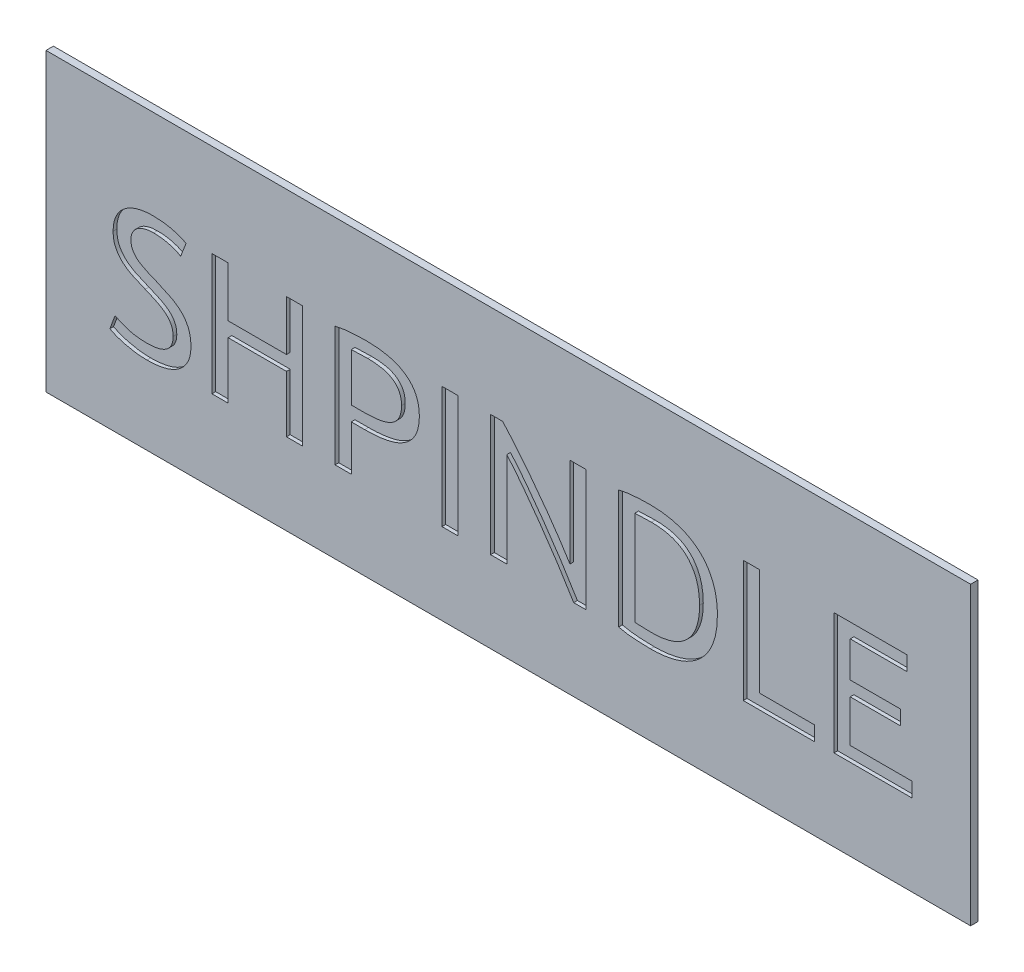
SolidWorks part; units mm, degrees
ref_plane "Front Plane" through (0, 0, 0) normal (0, 0, 1) x (1, 0, 0)
ref_plane "Top Plane" through (0, 0, 0) normal (0, 1, 0) x (1, 0, 0)
ref_plane "Right Plane" through (0, 0, 0) normal (1, 0, 0) x (0, 0, -1)
sketch "Sketch1" plane through (0, 0, 0) normal (0, 0, 1) x (1, 0, 0)
  line L1 (12.5, -4) -> (-12.5, -4)
  line L2 (12.5, -4) -> (12.5, 4)
  line L3 (12.5, 4) -> (-12.5, 4)
  line L4 (-12.5, -4) -> (-12.5, 4)
  line L5 (12.5, -4) -> (-12.5, 4) construction
  line L6 (12.5, 4) -> (-12.5, -4) construction
  point P0 (0, 0)
  dimension "D1" = 8
  dimension "D2" = 25
extrude "Boss-Extrude1" add sketch "Sketch1" along normal mid plane 0.2
sketch "Sketch2" plane through (0, 0, 0.1) normal (0, 0, 1) x (1, 0, 0)
  text T0 "SHPINDLE" font "Ubuntu" height in points 12
extrude "Cut-Extrude1" cut sketch "Sketch2" against normal blind 0.1
sketch "Sketch3" plane through (0, 0, 0.1) normal (0, 0, 1) x (1, 0, 0)
  text T0 "MOTOR  X" font "Ubuntu" height in points 12
extrude "Cut-Extrude2" [suppressed] cut sketch "Sketch3" against normal blind 0.1
sketch "Sketch4" [suppressed] plane through (0, 0, 0.1) normal (0, 0, 1) x (1, 0, 0)
  text T0 "MOTOR  Y" font "Ubuntu" height in points 12
extrude "Cut-Extrude3" [suppressed] cut sketch "Sketch4" against normal blind 0.1
sketch "Sketch5" [suppressed] plane through (0, 0, 0.1) normal (0, 0, 1) x (1, 0, 0)
  text T0 "Edge Sensors" font "Ubuntu" height in points 12
extrude "Cut-Extrude4" [suppressed] cut sketch "Sketch5" against normal blind 0.1
sketch "Sketch6" [suppressed] plane through (0, 0, 0.1) normal (0, 0, 1) x (1, 0, 0)
  text T0 "ON  LASER  OFF" font "Ubuntu" height in points 12
extrude "Cut-Extrude5" [suppressed] cut sketch "Sketch6" against normal blind 0.1
sketch "Sketch7" [suppressed] plane through (0, 0, 0.1) normal (0, 0, 1) x (1, 0, 0)
  text T0 "ON  PWR  OFF" font "Ubuntu" height in points 12
extrude "Cut-Extrude6" [suppressed] cut sketch "Sketch7" against normal blind 0.1
sketch "Sketch9" [suppressed] plane through (0, 0, 0.1) normal (0, 0, 1) x (1, 0, 0)
  text T0 "MOTOR  Z" font "Ubuntu" height in points 12
extrude "Cut-Extrude7" [suppressed] cut sketch "Sketch9" against normal blind 0.1
sketch "Sketch10" [suppressed] plane through (0, 0, 0.1) normal (0, 0, 1) x (1, 0, 0)
  text T0 "USB Device" font "Ubuntu" height in points 12
extrude "Cut-Extrude8" [suppressed] cut sketch "Sketch10" against normal blind 0.1
